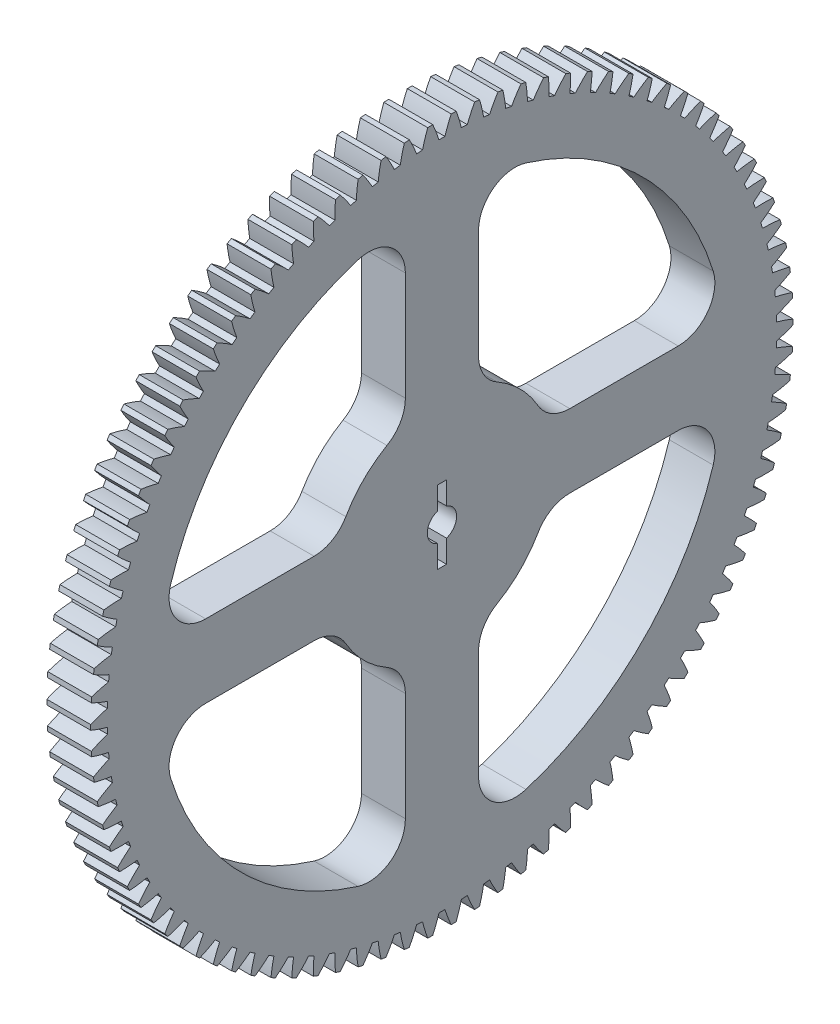
SolidWorks part; units mm, degrees
ref_plane "Plane1" through (0, 0, 0) normal (0, 0, 1) x (1, 0, 0)
ref_plane "Plane2" through (0, 0, 0) normal (0, 1, 0) x (1, 0, 0)
ref_plane "Plane3" through (0, 0, 0) normal (1, 0, 0) x (0, 0, -1)
sketch "HoldingSke" plane through (0, 0, 0) normal (0, 1, 0) x (1, 0, 0)
  line L0 (0, 0) -> (-0.0349, -0.4988)
  line L1 (-15, 0) -> (100, 0) construction
  line L2 (0, 0) -> (-2.1039, 2.3779)
  line L3 (0, 0) -> (-11.863, 4.5341)
  line L4 (0, 0) -> (-0.6024, 8.615)
  line L5 (0, 0) -> (-46.8476, -17.4728)
  line L6 (0, 0) -> (-9.9476, -6.7116)
  line L7 (-2.1039, 2.3779) -> (8.6586, 51.2059)
  line L8 (-76.2, 54.61) -> (-75.5, 54.61)
  line L9 (-71.009, 38.7566) -> (-53.1078, 45.2721)
  line L10 (-76.2, 71.12) -> (104.1128, 71.12)
  line L11 (0, 0) -> (-12, 0)
  line L12 (-76.2, 101.6) -> (-76.133, 101.6)
  line L13 (24.9733, 27.94) -> (52.9518, 28.4284)
  line L14 (24.9733, 27.94) -> (24.9743, 27.94)
  line L15 (24.9733, 27.94) -> (100.4006, 29.5858)
  line L16 (-63.627, -2) -> (-12.827, -2)
  circle A0 centre (0, 0) radius 2
  circle A1 centre (0, 0) radius 37.5
  circle A2 centre (0, 0) radius 37.5
  circle A3 centre (0, 0) radius 2
  dimension "MHD" = 75
  dimension "Hub_dia" = 75
  dimension "Bore" = 4
  dimension "MBD" = 4
  dimension "Num_teeth" = 94
  dimension "Pitch" = 0.5
  dimension "Overall_len" = 50
  dimension "Show_teeth" = 94
  dimension "Thickness" = 12
  dimension "OAL" = 50.0001
  dimension "T_dim" = 0.7
  dimension "Ap" = 20
  dimension "H" = 19.05
  dimension "Pitch_radius" = 180.3128
  dimension "Width" = 12
  dimension "Backlash" = 0.067
  dimension "Addendum_fac" = 1
  dimension "Dedendum_fac" = 1.25
  dimension "Clearance_fac" = 0.25
  dimension "Dedendum_add" = 0.001
  dimension "Module" = 2
sketch "BasProSke" plane through (0, 0, 0) normal (0, 1, 0) x (1, 0, 0)
  line L0 (-10, 0) -> (60, 0) construction
  line L1 (0, 0) -> (0, 96)
  line L2 (0, 0) -> (12, 0)
  line L3 (12, 0) -> (12, 96)
  line L4 (12, 96) -> (0, 96)
  dimension "Thickness" = 12
  dimension "Diameter" = 192
revolve "Base-Revolve" add sketch "BasProSke" angle 360 about L0
sketch "TooCutSke" plane through (0, 0, 0) normal (1, 0, 0) x (0, 0, -1)
  line L1 (0, 0) -> (0, 107) construction
  line L2 (0, 0) -> (-1.688, 93.9848) construction
  line L3 (0, 0) -> (-6.2813, 187.8726) construction
  line L4 (-1.688, 93.9848) -> (-3.1406, 93.9363) construction
  arc A0 (0.8174, 91.4953) -> (-0.8174, 91.4953) centre (0, 0) ccw
  arc A1 (2.5377, 95.9919) -> (-2.5377, 95.9919) centre (0, 0) ccw
  circle A2 centre (0, 0) radius 94 construction
  circle A3 centre (0, 0) radius 88.3311 construction
  arc A4 (-0.8174, 91.4953) -> (-2.5377, 95.9919) centre (-36.7231, 80.3356) ccw
  arc A5 (2.5377, 95.9919) -> (0.8174, 91.4953) centre (36.7231, 80.3356) ccw
  dimension "Root_dia" = 182.998
  dimension "Overcut_dia" = 192.0508
  dimension "Pitch_dia" = 188
  dimension "Base_dia" = 176.6622
  dimension "Flank_rad" = 37.6
  dimension "Half_ang" = 1.915
  dimension "Half_CT" = 1.4535
extrude "ToothCut" cut sketch "TooCutSke" along normal through all
fillet "Breaks" [suppressed] radius 0.04
fillet "RootFillets" [suppressed] radius 0.501
pattern_circular "TeethCuts" count 94 every 3.83 about axis through (-10, 0, 0) along (1, 0, 0) of "ToothCut", "RootFillets", "Breaks"
sketch "HubNeaOneSke" plane through (0, 0, 0) normal (-1, 0, 0) x (0, 0, 1)
  circle A0 centre (0, 0) radius 37.5
  dimension "Diameter" = 75
extrude "HubNearOne" [suppressed] add sketch "HubNeaOneSke" along normal blind 38.0001
sketch "HubNeaBotSke" plane through (0, 0, 0) normal (-1, 0, 0) x (0, 0, 1)
  circle A0 centre (0, 0) radius 37.5
  dimension "Diameter" = 75
extrude "HubNearBoth" [suppressed] add sketch "HubNeaBotSke" along normal blind 19
ref_plane "FarPln" through (12, 0, 0) normal (1, 0, 0) x (0, 0, -1)
sketch "HubFarSke" plane through (12, 0, 0) normal (1, 0, 0) x (0, 0, -1)
  circle A0 centre (0, 0) radius 37.5
  dimension "Diameter" = 75
extrude "HubFar" [suppressed] add sketch "HubFarSke" along normal blind 19
sketch "BorSke" plane through (0, 0, 0) normal (1, 0, 0) x (0, 0, -1)
  circle A0 centre (0, 0) radius 2
  dimension "Diameter" = 4
extrude "Bore" cut sketch "BorSke" along normal mid plane 100.0001
sketch "KeySke" plane through (0, 0, 0) normal (1, 0, 0) x (0, 0, -1)
  line L0 (-0.8, 0) -> (-0.8, 2.7)
  line L1 (-0.8, 2.7) -> (0.8, 2.7)
  line L2 (0.8, 2.7) -> (0.8, 0)
  line L3 (0, 0) -> (0, 34) construction
  line L4 (-0.8, 0) -> (0.8, 0)
  dimension "Offset" = 2.7
  dimension "Width" = 1.6
extrude "Keyway" [suppressed] cut sketch "KeySke" along normal mid plane 100.0001
pattern_circular "Keyway2" [suppressed] count 2 every 90 about axis through (-10, 0, 0) along (1, 0, 0)
sketch "Sketch1" plane through (12, 0, 0) normal (1, 0, 0) x (0, 0, -1)
  line L0 (-34.9486, 10) -> (-64.5889, 10)
  line L2 (-10, -64.5889) -> (-10, -34.9486)
  line L4 (10, -64.5889) -> (10, -34.9486)
  line L7 (64.5889, 10) -> (34.9486, 10)
  line L9 (64.5889, -10) -> (34.9486, -10)
  line L13 (-10, 34.9486) -> (-10, 64.5889)
  line L15 (10, 34.9486) -> (10, 64.5889)
  line L19 (-34.9486, -10) -> (-64.5889, -10)
  circle A0 centre (0, 0) radius 4
  arc A1 (-74.1414, -22.9579) -> (-22.9579, -74.1414) centre (0, 0) ccw
  arc A2 (-26.2693, -15.0331) -> (-15.0331, -26.2693) centre (0, 0) ccw
  arc A3 (-22.9579, 74.1414) -> (-74.1414, 22.9579) centre (0, 0) ccw
  arc A4 (-15.0331, 26.2693) -> (-26.2693, 15.0331) centre (0, 0) ccw
  arc A5 (26.2693, 15.0331) -> (15.0331, 26.2693) centre (0, 0) ccw
  arc A6 (15.0331, -26.2693) -> (26.2693, -15.0331) centre (0, 0) ccw
  arc A7 (22.9579, -74.1414) -> (74.1414, -22.9579) centre (0, 0) ccw
  arc A8 (74.1414, 22.9579) -> (22.9579, 74.1414) centre (0, 0) ccw
  arc A9 (10, -34.9486) -> (15.0331, -26.2693) centre (20, -34.9486) cw
  arc A10 (26.2693, -15.0331) -> (34.9486, -10) centre (34.9486, -20) cw
  arc A11 (64.5889, -10) -> (74.1414, -22.9579) centre (64.5889, -20) cw
  arc A12 (10, -64.5889) -> (22.9579, -74.1414) centre (20, -64.5889) ccw
  arc A13 (-64.5889, -10) -> (-74.1414, -22.9579) centre (-64.5889, -20) ccw
  arc A14 (-10, -64.5889) -> (-22.9579, -74.1414) centre (-20, -64.5889) cw
  arc A15 (-10, -34.9486) -> (-15.0331, -26.2693) centre (-20, -34.9486) ccw
  arc A16 (-26.2693, -15.0331) -> (-34.9486, -10) centre (-34.9486, -20) ccw
  arc A17 (-74.1414, 22.9579) -> (-64.5889, 10) centre (-64.5889, 20) ccw
  arc A18 (-34.9486, 10) -> (-26.2693, 15.0331) centre (-34.9486, 20) ccw
  arc A19 (-15.0331, 26.2693) -> (-10, 34.9486) centre (-20, 34.9486) ccw
  arc A20 (-10, 64.5889) -> (-22.9579, 74.1414) centre (-20, 64.5889) ccw
  arc A21 (34.9486, 10) -> (26.2693, 15.0331) centre (34.9486, 20) cw
  arc A22 (15.0331, 26.2693) -> (10, 34.9486) centre (20, 34.9486) cw
  arc A23 (10, 64.5889) -> (22.9579, 74.1414) centre (20, 64.5889) cw
  arc A24 (64.5889, 10) -> (74.1414, 22.9579) centre (64.5889, 20) ccw
  point P12 (10, -28.5669)
  point P26 (76.9677, -10)
  point P29 (10, -76.9677)
  point P38 (-28.5669, -10)
  point P45 (-10, 28.5669)
  point P48 (-10, 76.9677)
  point P51 (28.5669, 10)
  point P54 (10, 28.5669)
  point P59 (76.9677, 10)
  dimension "D1" = 8
  dimension "D4" = 10
  dimension "D2" = 20
  dimension "D3" = 20
extrude "Cut-Extrude1" cut sketch "Sketch1" against normal blind 26
sketch "Sketch2" plane through (12, 0, 0) normal (1, 0, 0) x (0, 0, -1)
  line L1 (-1.25, 10) -> (1.25, 10)
  line L2 (-1.25, 10) -> (-1.25, -10)
  line L3 (-1.25, -10) -> (1.25, -10)
  line L4 (1.25, 10) -> (1.25, -10)
  line L5 (-1.25, 10) -> (1.25, -10) construction
  line L6 (-1.25, -10) -> (1.25, 10) construction
  point P0 (0, 0)
  dimension "D1" = 20
  dimension "D2" = 2.5
extrude "Cut-Extrude2" cut sketch "Sketch2" against normal blind 26
equation "' \"Module@HoldingSke\" = 6.35"
equation "' \"Num_teeth@HoldingSke\" = 12"
equation "' \"Ap@HoldingSke\" =  20"
equation "' \"Ap@HoldingSke\" = 20"
equation "' \"Width@HoldingSke\" = 0.5 * 25.4"
equation "' \"Hub_dia@HoldingSke\"= 1 * 25.4"
equation "' \"Hub_dia@HoldingSke\" = 1 * 25.4"
equation "' \"Overall_len@HoldingSke\" = 1.0 * 25.4"
equation "' \"Bore@HoldingSke\" = 0.75 * 25.4"
equation "' \"T_dim@HoldingSke\" = 0.1 * 25.4"
equation "' \"Width@KeySke\" = 0.25 * 25.4"
equation "' \"Show_teeth@HoldingSke\" = 13"
equation "' \"Backlash@HoldingSke\" = 0.009 * 25.4"
equation "' \"Addendum_fac@HoldingSke\" = 1.0"
equation "' \"Dedendum_fac@HoldingSke\" = 1.25"
equation "' \"Dedendum_add@HoldingSke\" = 0.00005 * 25.4"
equation "' \"Clearance_fac@HoldingSke\" = 0.25"
equation "\"Pitch@HoldingSke\" = 1 / \"Module@HoldingSke\""
equation "\"Overcut_dia@TooCutSke\" = (\"Num_teeth@HoldingSke\" + 2 * \"Addendum_fac@HoldingSke\") / \"Pitch@HoldingSke\" + 0.002 * 25.4"
equation "\"Pitch_dia@TooCutSke\" = \"Num_teeth@HoldingSke\" / \"Pitch@HoldingSke\""
equation "\"Base_dia@TooCutSke\" = \"Num_teeth@HoldingSke\" / \"Pitch@HoldingSke\" * cos((\"Ap@HoldingSke\"  * 3.14159265 / 180))"
equation "\"Root_dia@TooCutSke\" = (\"Num_teeth@HoldingSke\" + 2) / \"Pitch@HoldingSke\" - 2 * (\"Addendum_fac@HoldingSke\" + \"Dedendum_fac@HoldingSke\") / \"Pitch@HoldingSke\" - \"Dedendum_add@HoldingSke\" * 2"
equation "\"Half_ang@TooCutSke\" = 180 / \"Num_teeth@HoldingSke\""
equation "\"Half_CT@TooCutSke\" = \"Num_teeth@HoldingSke\" / \"Pitch@HoldingSke\" * sin((3.14159265 / 2 / \"Num_teeth@HoldingSke\")) / 2 - 7 * \"Backlash@HoldingSke\" / 4"
equation "\"Flank_rad@TooCutSke\" = \"Num_teeth@HoldingSke\" / \"Pitch@HoldingSke\" / 5"
equation "\"Radius@RootFillets\" = \"Clearance_fac@HoldingSke\" / \"Pitch@HoldingSke\" + \"Dedendum_add@HoldingSke\""
equation "\"Break_rad@Breaks\" = 0.02 / \"Pitch@HoldingSke\""
equation "\"Thickness@HoldingSke\" = \"Width@HoldingSke\""
equation "\"OAL@HoldingSke\" = \"Thickness@HoldingSke\""
equation "\"MHD@HoldingSke\" = (\"Num_teeth@HoldingSke\" + 2) / \"Pitch@HoldingSke\" - 2 * (\"Addendum_fac@HoldingSke\" + \"Dedendum_fac@HoldingSke\")  / \"Pitch@HoldingSke\" - \"Dedendum_add@HoldingSke\" * 2"
equation "\"MBD@HoldingSke\" = (\"Num_teeth@HoldingSke\" + 2) / \"Pitch@HoldingSke\" - 2 * (\"Addendum_fac@HoldingSke\" + \"Dedendum_fac@HoldingSke\")  / \"Pitch@HoldingSke\" - \"Dedendum_add@HoldingSke\" * 2 - 0.002 * 25.4"
equation "\"MHD@HoldingSke\" = ((sgn( \"MHD@HoldingSke\" - \"Hub_dia@HoldingSke\" )-1)*( \"MHD@HoldingSke\" - \"Hub_dia@HoldingSke\" ))/-2+ \"Hub_dia@HoldingSke\""
equation "\"MBD@HoldingSke\" = ((sgn( \"MBD@HoldingSke\" - \"Bore@HoldingSke\" )-1)*( \"MBD@HoldingSke\" - \"Bore@HoldingSke\" ))/-2+ \"Bore@HoldingSke\""
equation "\"OAL@HoldingSke\" = ((sgn( \"OAL@HoldingSke\" - \"Overall_len@HoldingSke\" )+1)*( \"OAL@HoldingSke\" - \"Overall_len@HoldingSke\" ))/2 + \"Overall_len@HoldingSke\" + 0.000002 * 25.4"
equation "\"Num_teeth@TeethCuts\" = int( \"Show_teeth@HoldingSke\" ) + 1"
equation "\"Num_teeth@TeethCuts\" = ((sgn( \"Num_teeth@TeethCuts\" - \"Num_teeth@HoldingSke\" )-1)*( \"Num_teeth@TeethCuts\" - \"Num_teeth@HoldingSke\" ))/-2+ \"Num_teeth@HoldingSke\""
equation "\"Num_teeth@TeethCuts\" = ((sgn( \"Num_teeth@TeethCuts\" - 2.0)+1)*( \"Num_teeth@TeethCuts\" - 2.0))/2 +2.0"
equation "\"Angle@TeethCuts\" = 360.0 / \"Num_teeth@HoldingSke\""
equation "\"Diameter@BasProSke\" = (\"Num_teeth@HoldingSke\" + 2 * \"Addendum_fac@HoldingSke\") / \"Pitch@HoldingSke\""
equation "\"Thickness@BasProSke\"  = \"Thickness@HoldingSke\""
equation "' \"Fillet_rad@BasProSke\" =  \"Thickness@HoldingSke\" * 0.05"
equation "' \"Fillet_rad@BasProSke\" = \"Thickness@HoldingSke\" * 0.05"
equation "\"MHD@HoldingSke\" = ((sgn( \"MHD@HoldingSke\" - \"Root_dia@TooCutSke\" )-1)*( \"MHD@HoldingSke\" - \"Root_dia@TooCutSke\" ))/-2+ \"Root_dia@TooCutSke\""
equation "\"Diameter@HubNeaOneSke\" = \"MHD@HoldingSke\""
equation "\"Length@HubNearOne\" = \"OAL@HoldingSke\" - \"Thickness@BasProSke\""
equation "\"Diameter@HubNeaBotSke\" = \"MHD@HoldingSke\""
equation "\"Length@HubNearBoth\" = ( \"OAL@HoldingSke\" - \"Thickness@BasProSke\" ) / 2.0"
equation "\"Thickness@FarPln\" = \"Thickness@BasProSke\""
equation "\"Diameter@HubFarSke\" = \"MHD@HoldingSke\""
equation "\"Length@HubFar\" = ( \"OAL@HoldingSke\" - \"Thickness@BasProSke\" ) / 2.0"
equation "\"Diameter@BorSke\" = \"MBD@HoldingSke\""
equation "\"D1@Bore\" = \"OAL@HoldingSke\" * 2.0"
equation "\"D1@Keyway\" = \"OAL@HoldingSke\" * 2.0"
equation "\"Offset@KeySke\" = \"T_dim@HoldingSke\" + \"MBD@HoldingSke\" / 2.0"
